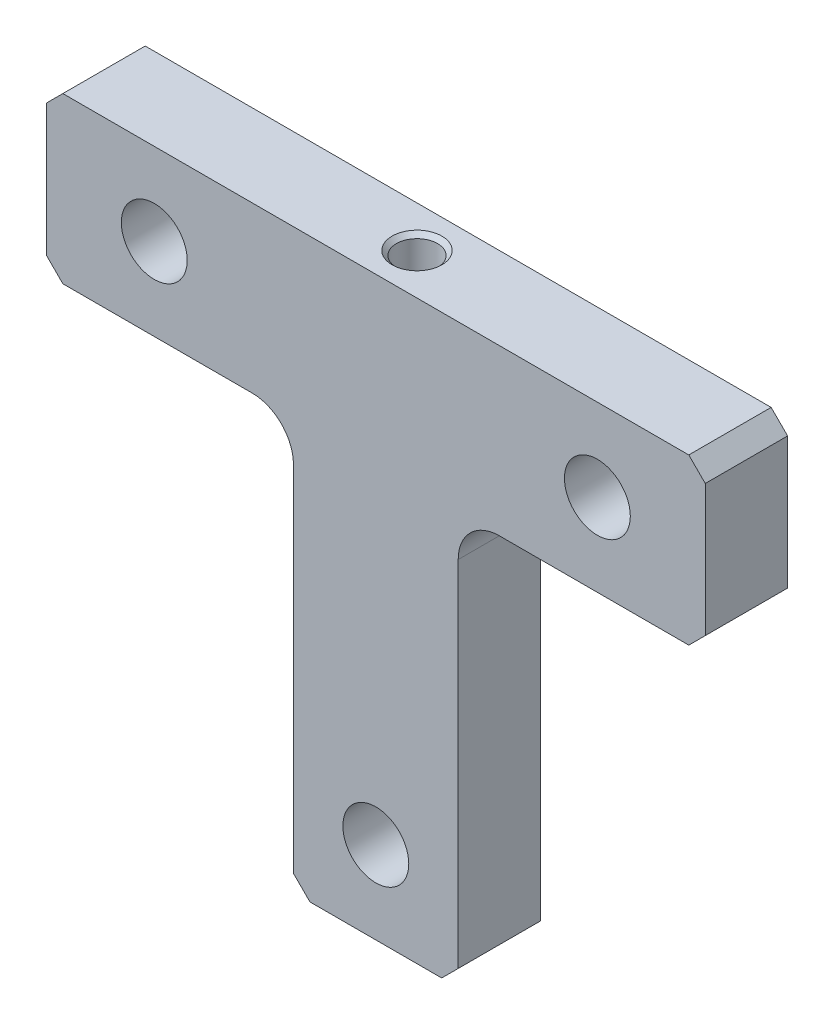
SolidWorks part; units mm, degrees
material "AISI 304"
ref_plane "Front Plane" through (0, 0, 0) normal (0, 0, 1) x (1, 0, 0)
ref_plane "Top Plane" through (0, 0, 0) normal (0, 1, 0) x (1, 0, 0)
ref_plane "Right Plane" through (0, 0, 0) normal (1, 0, 0) x (0, 0, -1)
sketch "Sketch1" plane through (0, 0, 0) normal (0, 0, 1) x (1, 0, 0)
  line L0 (-10, -10) -> (-10, 40)
  line L1 (-10, 40) -> (-40, 40)
  line L2 (-40, 40) -> (-40, 60)
  line L3 (-40, 60) -> (40, 60)
  line L4 (40, 60) -> (40, 40)
  line L5 (40, 40) -> (10, 40)
  line L6 (10, 40) -> (10, -10)
  line L7 (10, -10) -> (-10, -10)
  dimension "D1" = 20
  dimension "D2" = 10
  dimension "D3" = 20
  dimension "D4" = 10
  dimension "D5" = 70
  dimension "D6" = 40
  dimension "D7" = 40
extrude "Profile Shape" add sketch "Sketch1" along normal mid plane 10
sketch "Sketch2" plane through (0, 0, 5) normal (0, 0, 1) x (1, 0, 0)
  circle A0 centre (0, 0) radius 4
  dimension "D1" = 8
extrude "Lower Hole" cut sketch "Sketch2" against normal through all
sketch "Sketch3" plane through (0, 0, 5) normal (0, 0, 1) x (1, 0, 0)
  circle A0 centre (26.9, 50) radius 4
  dimension "D3" = 8
  dimension "D1" = 50
  dimension "D2" = 26.9
extrude "Upper Hole Right" cut sketch "Sketch3" against normal through all
mirror "Upper Hole Left" about plane through (0, 0, 0) normal (1, 0, 0) of "Upper Hole Right"
hole_wizard "M6 Tapped Hole Top" positions "Sketch4" profile "Sketch5" tap size "M6" standard "ISO"
sketch "Sketch4" plane through (0, 60, 0) normal (0, 1, 0) x (1, 0, 0)
  point P0 (0, 0)
sketch "Sketch5" plane through (0, 60, 0) normal (1, 0, 0) x (0, 0, 1)
  line L0 (0, 0) -> (0, 16.5022)
  line L1 (0, 16.5022) -> (2.5, 15)
  line L2 (2.5, 15) -> (2.5, 0.525)
  line L3 (2.5, 0.525) -> (3.025, 0)
  line L5 (3.025, 0) -> (0, 0)
  line L6 (-2.5, 0.525) -> (-3.025, 0) construction
  line L10 (0, 16.5022) -> (-2.5, 15) construction
  line L11 (0, -6.35) -> (0, 107.95) construction
  dimension "Tap Drill Dia." = 5
  dimension "Tap Drill Depth" = 15
  dimension "Near C'Sink Dia." = 6.05
  dimension "Near C'Sink Angle" = 90
  dimension "Drill Angle" = 118
cosmetic thread "Hole Thread1" parameters "D1"=12, "D2"=6
chamfer "External Edges" distance 2 angle 45 6 edges at (40, 60, 0) (40, 40, 0) (-40, 60, 0) (-40, 40, 0) (-10, -10, 0) (10, -10, 0)
fillet "Internal Edges" radius 5 2 edges at (-10, 40, 0) (10, 40, 0)
